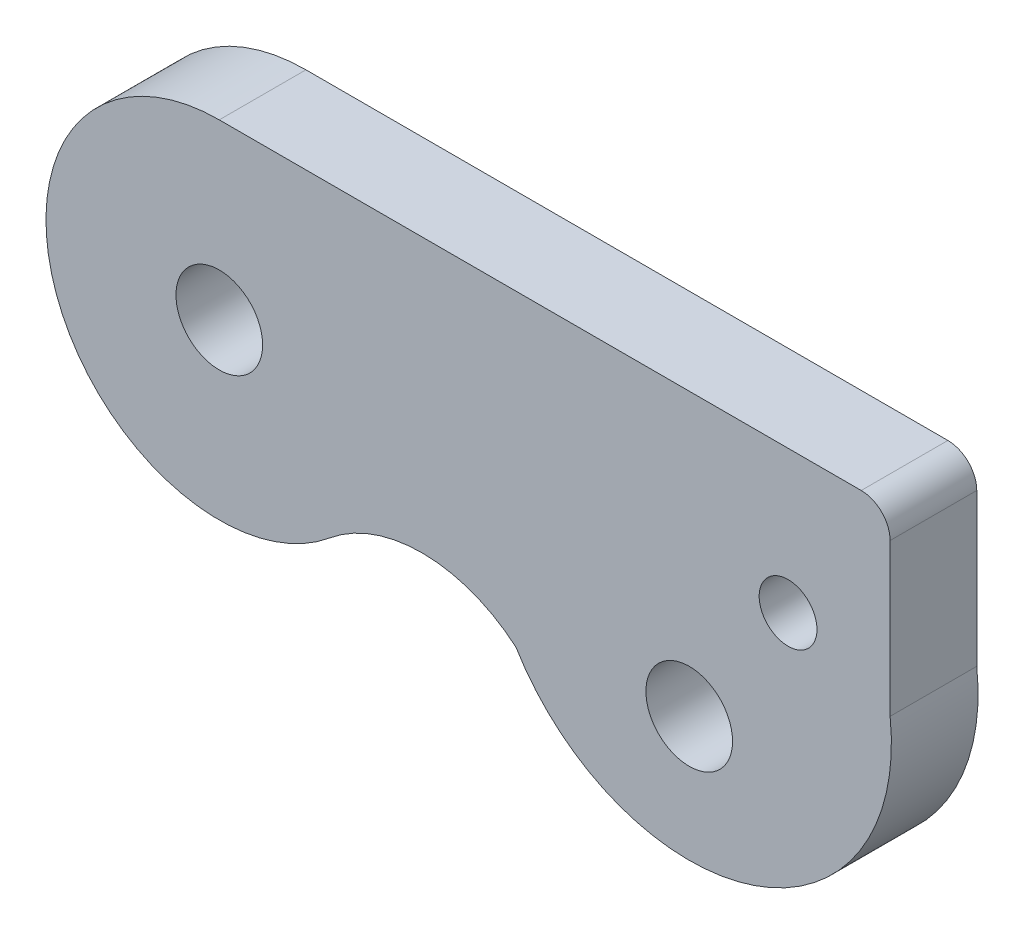
SolidWorks part; units mm, degrees
material "Acrylic (Medium-high impact)"
ref_plane "Front Plane" through (0, 0, 0) normal (0, 0, 1) x (1, 0, 0)
ref_plane "Top Plane" through (0, 0, 0) normal (0, 1, 0) x (1, 0, 0)
ref_plane "Right Plane" through (0, 0, 0) normal (1, 0, 0) x (0, 0, -1)
sketch "Sketch1" plane through (0, 0, 0) normal (0, 0, 1) x (1, 0, 0)
  line L0 (0, 0) -> (22, 0)
  line L4 (16.2688, 3.5647) -> (16.2688, -9.748) construction
  line L5 (16.2688, -9.748) -> (19.6906, -4.9362) construction
  line L6 (23.2234, -6.272) -> (23.2234, -1)
  line L7 (22, 0) -> (22.2234, 0)
  arc A0 (0, 0) -> (3.8273, -10.6208) centre (0, -6) ccw
  arc A1 (3.8273, -10.6208) -> (10.2692, -10.674) centre (7.0167, -14.4715) cw
  arc A2 (10.2692, -10.674) -> (23.2234, -6.272) centre (16.2688, -7.0677) ccw
  circle A4 centre (0, -6) radius 1.5
  arc A7 (23.2234, -1) -> (22.2234, 0) centre (22.2234, -1) ccw
  circle A8 centre (19.6906, -4.9362) radius 1
  circle A9 centre (16.2688, -9.748) radius 1.5
  dimension "D2" = 6
  dimension "D4" = 5
  dimension "D6" = 7
  dimension "D8" = 3
  dimension "D10" = 35.418
  dimension "D11" = 5.9045
  dimension "D13" = 1
  dimension "D9" = 2
  dimension "D1" = 22
  dimension "D3" = 23
  dimension "D5" = 7
  dimension "D7" = 19
extrude "Boss-Extrude1" add sketch "Sketch1" along normal blind 3
